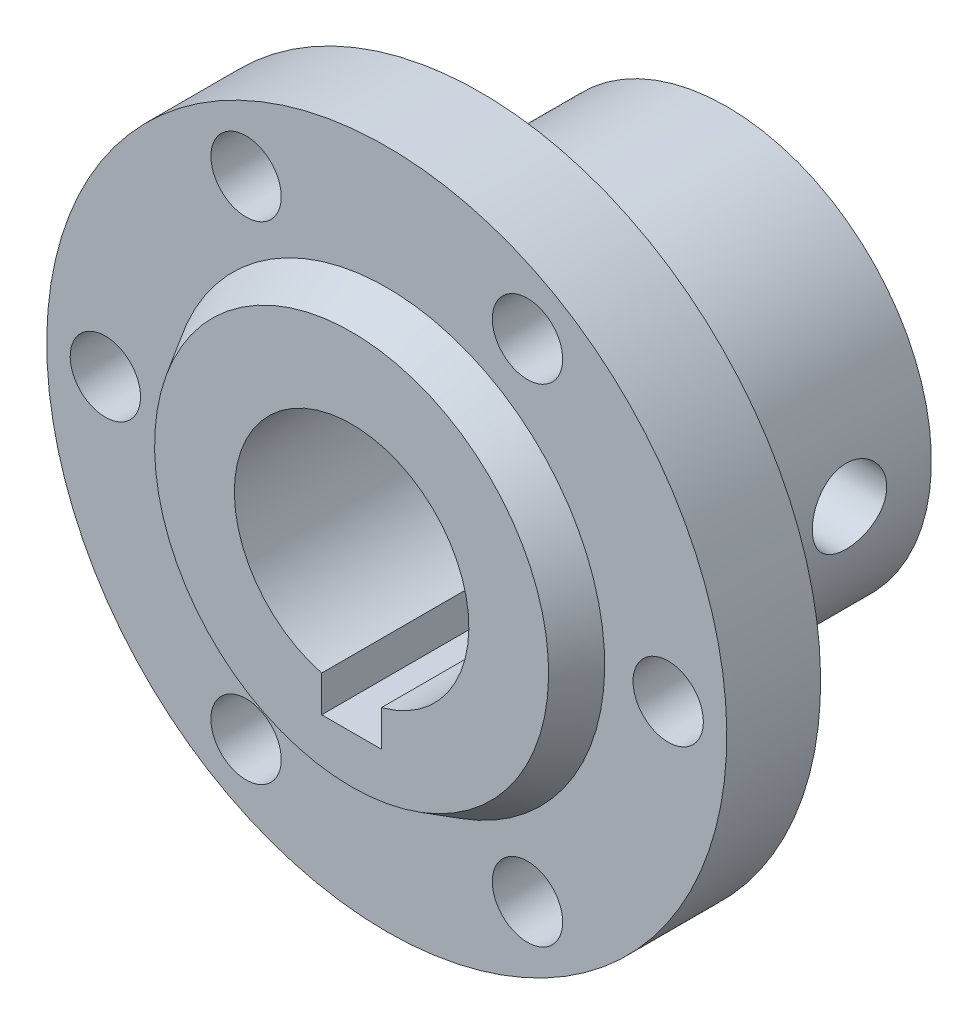
SolidWorks part; units mm, degrees
ref_plane "Front Plane" through (0, 0, 0) normal (0, 0, 1) x (1, 0, 0)
ref_plane "Top Plane" through (0, 0, 0) normal (0, 1, 0) x (1, 0, 0)
ref_plane "Right Plane" through (0, 0, 0) normal (1, 0, 0) x (0, 0, -1)
sketch "Sketch1" plane through (0, 0, 0) normal (1, 0, 0) x (0, 0, -1)
  line L0 (-11, 0) -> (21, 0) construction
  line L1 (21, 0) -> (21, 17.45) construction
  line L2 (21, 17.45) -> (7.03, 17.45)
  line L3 (7.03, 17.45) -> (7.03, 18.5)
  line L4 (7.03, 18.5) -> (0, 18.5)
  line L6 (0, 18.5) -> (0, 29)
  line L8 (0, 29) -> (-8, 29)
  line L9 (-8, 29) -> (-8, 18.5862)
  line L11 (-8, 18.5862) -> (-11, 16.8032)
  line L12 (-11, 16.8032) -> (-11, 0) construction
  line L13 (-11, 10) -> (21, 10)
  line L14 (-11, 10) -> (-11, 16.8032)
  line L15 (21, 10) -> (21, 17.45)
  dimension "D1" = 10
  dimension "D2" = 29
  dimension "D3" = 18.5
  dimension "D4" = 17.45
  dimension "D5" = 13.97
  dimension "D6" = 6.8032
  dimension "D7" = 8
revolve "Revolve1" add sketch "Sketch1" angle 360 about L0
sketch "Sketch2" plane through (0, 0, 0) normal (0, 0, 1) x (1, 0, 0)
  line L0 (0, 0) -> (0, -12.75) construction
  line L1 (-2.55, -12.75) -> (2.55, -12.75)
  line L2 (-2.55, -12.75) -> (-2.55, -9.6694)
  line L3 (2.55, -12.75) -> (2.55, -9.6694)
  circle A0 centre (0, 0) radius 10 construction
  arc A1 (-2.55, -9.6694) -> (2.55, -9.6694) centre (0, 0) ccw
  point P6 (0, -12.75)
  point P12 (2.55, -12.75)
  dimension "D1" = 12.75
  dimension "D2" = 5.1
extrude "Cut-Extrude1" cut sketch "Sketch2" against normal through all both and the other way through all
sketch "Sketch3" plane through (0, 0, 0) normal (0, 0, -1) x (-1, 0, 0)
  circle A0 centre (0, 0) radius 24 construction
  circle A1 centre (-24, 0) radius 3
  circle A2 centre (0, 0) radius 24 construction
  circle A3 centre (-12, 20.7846) radius 3
  circle A4 centre (0, 0) radius 24 construction
  circle A5 centre (12, 20.7846) radius 3
  circle A6 centre (0, 0) radius 24 construction
  circle A7 centre (24, 0) radius 3
  circle A8 centre (0, 0) radius 24 construction
  circle A9 centre (12, -20.7846) radius 3
  circle A10 centre (0, 0) radius 24 construction
  circle A11 centre (-12, -20.7846) radius 3
  dimension "D1" = 6
  dimension "D3" = 48
  dimension "D2" = 6
extrude "Cut-Extrude2" cut sketch "Sketch3" against normal through all both and the other way through all
sketch "Sketch4" plane through (0, 0, 0) normal (1, 0, 0) x (0, -1, 0)
  line L0 (0, 21) -> (0, 7.03) construction
  line L2 (18.5, 7.03) -> (-18.5, 7.03) construction
  line L3 (0, 14.015) -> (17.45, 14.015) construction
  line L4 (17.45, 7.03) -> (17.45, 21) construction
  circle A0 centre (0, 14.015) radius 3.175
  dimension "D1" = 6.35
extrude "Cut-Extrude3" cut sketch "Sketch4" against normal through all both and the other way through all
